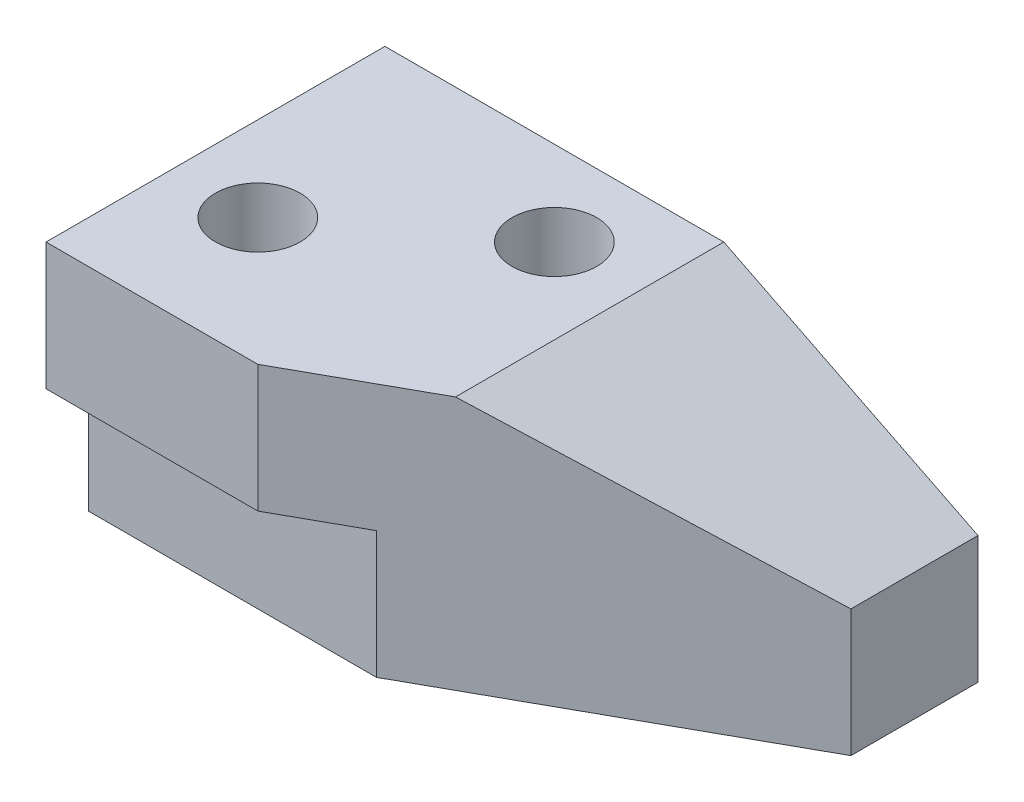
SolidWorks part; units mm, degrees
ref_plane "Front Plane" through (0, 0, 0) normal (0, 0, 1) x (1, 0, 0)
ref_plane "Top Plane" through (0, 0, 0) normal (0, 1, 0) x (1, 0, 0)
ref_plane "Right Plane" through (0, 0, 0) normal (1, 0, 0) x (0, 0, -1)
sketch "Sketch1" plane through (0, 0, 0) normal (0, 1, 0) x (1, 0, 0)
  line L1 (0, 0) -> (70, 0)
  line L2 (0, 0) -> (0, 40)
  line L3 (0, 40) -> (70, 40)
  line L4 (70, 0) -> (70, 40)
  dimension "D1" = 70
  dimension "D2" = 40
extrude "Boss-Extrude1" add sketch "Sketch1" along normal blind 30
sketch "Sketch2" plane through (0, 0, 0) normal (0, 0, 1) x (1, 0, 0)
  line L0 (70, 30) -> (40, 30)
  line L1 (0, 30) -> (70, 30) construction
  line L2 (40, 30) -> (70, 15)
  line L3 (70, 30) -> (70, 0) construction
  line L4 (70, 15) -> (70, 30)
  dimension "D1" = 30
  dimension "D2" = 15
extrude "Cut-Extrude1" cut sketch "Sketch2" against normal through all
sketch "Sketch4" plane through (0, 0, 0) normal (0, -1, 0) x (-1, 0, 0)
  line L0 (0, 0) -> (-25, 0) construction
  line L1 (0, 0) -> (-70, 0) construction
  line L2 (-25, 0) -> (-70, 25)
  line L3 (-70, 0) -> (-70, 40) construction
  line L4 (-70, 25) -> (-70, 0)
  line L5 (-70, 0) -> (-25, 0)
  dimension "D1" = 25
  dimension "D2" = 25
extrude "Cut-Extrude2" cut sketch "Sketch4" against normal through all contours L5 L2 L4
sketch "Sketch5" plane through (0, 0, 0) normal (-1, 0, 0) x (0, 0, 1)
  line L1 (0, 0) -> (-5, 0)
  line L2 (0, 0) -> (0, 15)
  line L3 (0, 15) -> (-5, 15)
  line L4 (-5, 0) -> (-5, 15)
  dimension "D1" = 15
  dimension "D2" = 5
extrude "Cut-Extrude3" cut sketch "Sketch5" against normal through all
sketch "Sketch6" plane through (0, 30, 0) normal (0, 1, 0) x (1, 0, 0)
  line L0 (0, 0) -> (10, 0) construction
  line L1 (0, 0) -> (25, 0) construction
  line L2 (10, 0) -> (10, 15) construction
  circle A0 centre (10, 15) radius 5
  dimension "D3" = 10
  dimension "D1" = 10
  dimension "D2" = 15
extrude "Cut-Extrude4" cut sketch "Sketch6" against normal through all contours A0
sketch "Sketch7" plane through (0, 30, 0) normal (0, 1, 0) x (1, 0, 0)
  line L0 (40, 40) -> (30, 40) construction
  line L1 (40, 40) -> (0, 40) construction
  line L2 (30, 40) -> (30, 30) construction
  circle A0 centre (30, 30) radius 5
  dimension "D3" = 10
  dimension "D1" = 10
  dimension "D2" = 10
extrude "Cut-Extrude5" cut sketch "Sketch7" against normal through all contours A0
